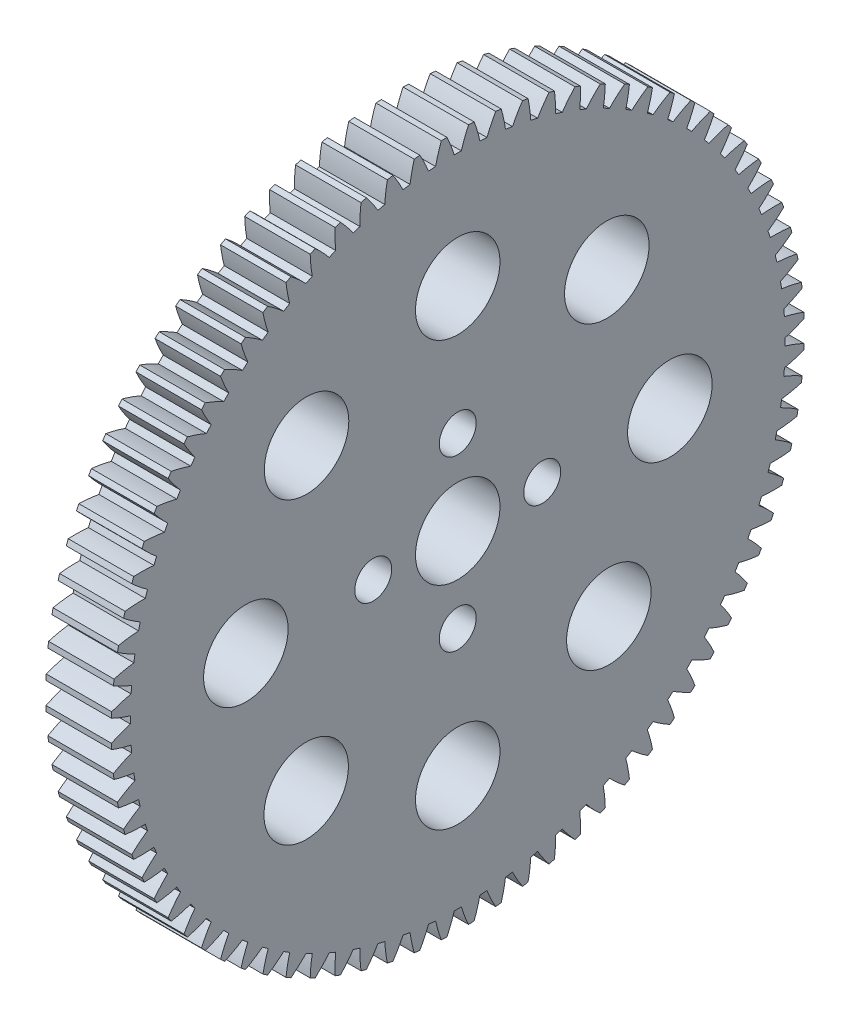
SolidWorks part; units mm, degrees
material "6061 Alloy"
ref_plane "Plane1" through (0, 0, 0) normal (0, 0, 1) x (1, 0, 0)
ref_plane "Plane2" through (0, 0, 0) normal (0, 1, 0) x (1, 0, 0)
ref_plane "Plane3" through (0, 0, 0) normal (1, 0, 0) x (0, 0, -1)
sketch "HoldingSke" plane through (0, 0, 0) normal (0, 1, 0) x (1, 0, 0)
  line L0 (0, 0) -> (0.2171, -1.231)
  line L1 (-15, 0) -> (100, 0) construction
  line L2 (0, 0) -> (-2.1039, 2.3779)
  line L3 (0, 0) -> (-11.863, 4.5341)
  line L4 (0, 0) -> (1.4996, 8.5048)
  line L5 (0, 0) -> (-46.8476, -17.4728)
  line L6 (0, 0) -> (-5.1396, -3.4677)
  line L7 (-2.1039, 2.3779) -> (8.6586, 51.2059)
  line L8 (-76.2, 54.61) -> (-74.8, 54.61)
  line L9 (-71.009, 38.7566) -> (-53.1078, 45.2721)
  line L10 (-76.2, 71.12) -> (104.1128, 71.12)
  line L11 (0, 0) -> (-6.2, 0)
  line L12 (-76.2, 101.6) -> (-76.17, 101.6)
  line L13 (24.9733, 27.94) -> (52.9518, 28.4284)
  line L14 (24.9733, 27.94) -> (24.9743, 27.94)
  line L15 (24.9733, 27.94) -> (100.4006, 29.5858)
  line L16 (-63.627, -0.8) -> (-12.827, -0.8)
  circle A0 centre (0, 0) radius 4
  circle A1 centre (0, 0) radius 30.999
  circle A2 centre (0, 0) radius 37.5
  circle A3 centre (0, 0) radius 4
  dimension "MHD" = 61.998
  dimension "Hub_dia" = 75
  dimension "Bore" = 8
  dimension "MBD" = 8
  dimension "Num_teeth" = 80
  dimension "Pitch_radius" = 180.3128
  dimension "Pitch" = 1.25
  dimension "Width" = 6.2
  dimension "Overall_len" = 50
  dimension "Show_teeth" = 80
  dimension "Thickness" = 6.2
  dimension "OAL" = 50.0001
  dimension "T_dim" = 1.4
  dimension "Ap" = 20
  dimension "H" = 19.05
  dimension "Backlash" = 0.03
  dimension "Addendum_fac" = 1
  dimension "Dedendum_fac" = 1.25
  dimension "Clearance_fac" = 0.25
  dimension "Dedendum_add" = 0.001
  dimension "Module" = 0.8
sketch "BasProSke" plane through (0, 0, 0) normal (0, 1, 0) x (1, 0, 0)
  line L0 (-10, 0) -> (60, 0) construction
  line L1 (0, 0) -> (0, 32.8)
  line L2 (0, 0) -> (6.2, 0)
  line L3 (6.2, 0) -> (6.2, 32.8)
  line L4 (6.2, 32.8) -> (0, 32.8)
  dimension "Diameter" = 65.6
  dimension "Thickness" = 6.2
revolve "Base-Revolve" add sketch "BasProSke" angle 360 about L0
sketch "TooCutSke" plane through (0, 0, 0) normal (1, 0, 0) x (0, 0, -1)
  line L1 (0, 0) -> (0, 107) construction
  line L2 (0, 0) -> (-0.6808, 31.9928) construction
  line L3 (0, 0) -> (-2.5122, 63.9403) construction
  line L4 (-0.6808, 31.9928) -> (-1.2561, 31.9702) construction
  arc A0 (0.3357, 30.9972) -> (-0.3357, 30.9972) centre (0, 0) ccw
  arc A1 (1.0352, 32.8091) -> (-1.0352, 32.8091) centre (0, 0) ccw
  circle A2 centre (0, 0) radius 32 construction
  circle A3 centre (0, 0) radius 30.0702 construction
  arc A4 (-0.3357, 30.9972) -> (-1.0352, 32.8091) centre (-12.5921, 27.3066) ccw
  arc A5 (1.0352, 32.8091) -> (0.3357, 30.9972) centre (12.5921, 27.3066) ccw
  dimension "Root_dia" = 61.998
  dimension "Overcut_dia" = 65.6508
  dimension "Pitch_dia" = 64
  dimension "Base_dia" = 60.1403
  dimension "Flank_rad" = 12.8
  dimension "Half_ang" = 2.25
  dimension "Half_CT" = 0.5758
extrude "ToothCut" cut sketch "TooCutSke" along normal through all
fillet "Breaks" [suppressed] radius 0.016
fillet "RootFillets" [suppressed] radius 0.201
pattern_circular "TeethCuts" count 80 every 4.5 about axis through (-10, 0, 0) along (1, 0, 0) of "ToothCut", "RootFillets", "Breaks"
sketch "HubNeaOneSke" plane through (0, 0, 0) normal (-1, 0, 0) x (0, 0, 1)
  circle A0 centre (0, 0) radius 30.999
  dimension "Diameter" = 61.998
extrude "HubNearOne" [suppressed] add sketch "HubNeaOneSke" along normal blind 43.8001
sketch "HubNeaBotSke" plane through (0, 0, 0) normal (-1, 0, 0) x (0, 0, 1)
  circle A0 centre (0, 0) radius 30.999
  dimension "Diameter" = 61.998
extrude "HubNearBoth" [suppressed] add sketch "HubNeaBotSke" along normal blind 21.9
ref_plane "FarPln" through (6.2, 0, 0) normal (1, 0, 0) x (0, 0, -1)
sketch "HubFarSke" plane through (6.2, 0, 0) normal (1, 0, 0) x (0, 0, -1)
  circle A0 centre (0, 0) radius 30.999
  dimension "Diameter" = 61.998
extrude "HubFar" [suppressed] add sketch "HubFarSke" along normal blind 21.9
sketch "BorSke" plane through (0, 0, 0) normal (1, 0, 0) x (0, 0, -1)
  circle A0 centre (0, 0) radius 4
  dimension "Diameter" = 8
extrude "Bore" cut sketch "BorSke" along normal mid plane 100.0001
sketch "KeySke" plane through (0, 0, 0) normal (1, 0, 0) x (0, 0, -1)
  line L0 (-1.5, 0) -> (-1.5, 5.4)
  line L1 (-1.5, 5.4) -> (1.5, 5.4)
  line L2 (1.5, 5.4) -> (1.5, 0)
  line L3 (0, 0) -> (0, 34) construction
  line L4 (-1.5, 0) -> (1.5, 0)
  dimension "Offset" = 5.4
  dimension "Width" = 3
extrude "Keyway" [suppressed] cut sketch "KeySke" along normal mid plane 100.0001
pattern_circular "Keyway2" [suppressed] count 2 every 90 about axis through (-10, 0, 0) along (1, 0, 0)
sketch "Sketch1" plane through (6.2, 0, 0) normal (1, 0, 0) x (0, 0, -1)
  line L0 (0, 0) -> (28.2252, 28.7327) construction
  line L1 (0, 0) -> (-25.3201, -24.9439) construction
  line L2 (0, 0) -> (24.7366, -24.4515) construction
  line L3 (0, 0) -> (-25.836, 25.5556) construction
  circle A0 centre (0, 20.084) radius 4
  circle A1 centre (0, -20.0633) radius 4
  circle A2 centre (20.084, 0) radius 4
  circle A3 centre (-20.0633, 0) radius 4
  circle A4 centre (14.1126, 14.3663) radius 4
  circle A5 centre (14.3069, -14.142) radius 4
  circle A6 centre (-14.3483, -14.1351) radius 4
  circle A7 centre (-14.315, 14.1597) radius 4
  circle A8 centre (0, 8) radius 1.75
  circle A9 centre (0, -8) radius 1.75
  circle A10 centre (8, 0) radius 1.75
  circle A11 centre (-8, 0) radius 1.75
  dimension "D1" = 8
  dimension "D2" = 8
  dimension "D3" = 8
  dimension "D4" = 8
  dimension "D5" = 8
  dimension "D6" = 8
  dimension "D7" = 8
  dimension "D8" = 8
  dimension "D17" = 3.5
  dimension "D18" = 3.5
  dimension "D19" = 3.5
  dimension "D20" = 3.5
  dimension "D9" = 12.7
  dimension "D10" = 12.7
  dimension "D11" = 12.7
  dimension "D12" = 12.7
  dimension "D13" = 12.7
  dimension "D14" = 12.7
  dimension "D15" = 12.7
  dimension "D16" = 12.7
  dimension "D21" = 8
  dimension "D22" = 8
  dimension "D23" = 8
  dimension "D24" = 8
extrude "Cut-Extrude1" cut sketch "Sketch1" against normal through all
equation "' \"Module@HoldingSke\" = 6.35"
equation "' \"Num_teeth@HoldingSke\" = 12"
equation "' \"Ap@HoldingSke\" =  20"
equation "' \"Width@HoldingSke\" = 0.5 * 25.4"
equation "' \"Hub_dia@HoldingSke\"= 1 * 25.4"
equation "' \"Overall_len@HoldingSke\" = 1.0 * 25.4"
equation "' \"Bore@HoldingSke\" = 0.75 * 25.4"
equation "' \"T_dim@HoldingSke\" = 0.1 * 25.4"
equation "' \"Width@KeySke\" = 0.25 * 25.4"
equation "' \"Show_teeth@HoldingSke\" = 13"
equation "' \"Backlash@HoldingSke\" = 0.009 * 25.4"
equation "' \"Addendum_fac@HoldingSke\" = 1.0"
equation "' \"Dedendum_fac@HoldingSke\" = 1.25"
equation "' \"Dedendum_add@HoldingSke\" = 0.00005 * 25.4"
equation "' \"Clearance_fac@HoldingSke\" = 0.25"
equation "\"Pitch@HoldingSke\" = 1 / \"Module@HoldingSke\""
equation "\"Overcut_dia@TooCutSke\" = (\"Num_teeth@HoldingSke\" + 2 * \"Addendum_fac@HoldingSke\") / \"Pitch@HoldingSke\" + 0.002 * 25.4"
equation "\"Pitch_dia@TooCutSke\" = \"Num_teeth@HoldingSke\" / \"Pitch@HoldingSke\""
equation "\"Base_dia@TooCutSke\" = \"Num_teeth@HoldingSke\" / \"Pitch@HoldingSke\" * cos((\"Ap@HoldingSke\"  * 3.14159265 / 180))"
equation "\"Root_dia@TooCutSke\" = (\"Num_teeth@HoldingSke\" + 2) / \"Pitch@HoldingSke\" - 2 * (\"Addendum_fac@HoldingSke\" + \"Dedendum_fac@HoldingSke\") / \"Pitch@HoldingSke\" - \"Dedendum_add@HoldingSke\" * 2"
equation "\"Half_ang@TooCutSke\" = 180 / \"Num_teeth@HoldingSke\""
equation "\"Half_CT@TooCutSke\" = \"Num_teeth@HoldingSke\" / \"Pitch@HoldingSke\" * sin((3.14159265 / 2 / \"Num_teeth@HoldingSke\")) / 2 - 7 * \"Backlash@HoldingSke\" / 4"
equation "\"Flank_rad@TooCutSke\" = \"Num_teeth@HoldingSke\" / \"Pitch@HoldingSke\" / 5"
equation "\"Radius@RootFillets\" = \"Clearance_fac@HoldingSke\" / \"Pitch@HoldingSke\" + \"Dedendum_add@HoldingSke\""
equation "\"Break_rad@Breaks\" = 0.02 / \"Pitch@HoldingSke\""
equation "\"Thickness@HoldingSke\" = \"Width@HoldingSke\""
equation "\"OAL@HoldingSke\" = \"Thickness@HoldingSke\""
equation "\"MHD@HoldingSke\" = (\"Num_teeth@HoldingSke\" + 2) / \"Pitch@HoldingSke\" - 2 * (\"Addendum_fac@HoldingSke\" + \"Dedendum_fac@HoldingSke\")  / \"Pitch@HoldingSke\" - \"Dedendum_add@HoldingSke\" * 2"
equation "\"MBD@HoldingSke\" = (\"Num_teeth@HoldingSke\" + 2) / \"Pitch@HoldingSke\" - 2 * (\"Addendum_fac@HoldingSke\" + \"Dedendum_fac@HoldingSke\")  / \"Pitch@HoldingSke\" - \"Dedendum_add@HoldingSke\" * 2 - 0.002 * 25.4"
equation "\"MHD@HoldingSke\" = ((sgn( \"MHD@HoldingSke\" - \"Hub_dia@HoldingSke\" )-1)*( \"MHD@HoldingSke\" - \"Hub_dia@HoldingSke\" ))/-2+ \"Hub_dia@HoldingSke\""
equation "\"MBD@HoldingSke\" = ((sgn( \"MBD@HoldingSke\" - \"Bore@HoldingSke\" )-1)*( \"MBD@HoldingSke\" - \"Bore@HoldingSke\" ))/-2+ \"Bore@HoldingSke\""
equation "\"OAL@HoldingSke\" = ((sgn( \"OAL@HoldingSke\" - \"Overall_len@HoldingSke\" )+1)*( \"OAL@HoldingSke\" - \"Overall_len@HoldingSke\" ))/2 + \"Overall_len@HoldingSke\" + 0.000002 * 25.4"
equation "\"Num_teeth@TeethCuts\" = int( \"Show_teeth@HoldingSke\" ) + 1"
equation "\"Num_teeth@TeethCuts\" = ((sgn( \"Num_teeth@TeethCuts\" - \"Num_teeth@HoldingSke\" )-1)*( \"Num_teeth@TeethCuts\" - \"Num_teeth@HoldingSke\" ))/-2+ \"Num_teeth@HoldingSke\""
equation "\"Num_teeth@TeethCuts\" = ((sgn( \"Num_teeth@TeethCuts\" - 2.0)+1)*( \"Num_teeth@TeethCuts\" - 2.0))/2 +2.0"
equation "\"Angle@TeethCuts\" = 360.0 / \"Num_teeth@HoldingSke\""
equation "\"Diameter@BasProSke\" = (\"Num_teeth@HoldingSke\" + 2 * \"Addendum_fac@HoldingSke\") / \"Pitch@HoldingSke\""
equation "\"Thickness@BasProSke\"  = \"Thickness@HoldingSke\""
equation "' \"Fillet_rad@BasProSke\" =  \"Thickness@HoldingSke\" * 0.05"
equation "\"MHD@HoldingSke\" = ((sgn( \"MHD@HoldingSke\" - \"Root_dia@TooCutSke\" )-1)*( \"MHD@HoldingSke\" - \"Root_dia@TooCutSke\" ))/-2+ \"Root_dia@TooCutSke\""
equation "\"Diameter@HubNeaOneSke\" = \"MHD@HoldingSke\""
equation "\"Length@HubNearOne\" = \"OAL@HoldingSke\" - \"Thickness@BasProSke\""
equation "\"Diameter@HubNeaBotSke\" = \"MHD@HoldingSke\""
equation "\"Length@HubNearBoth\" = ( \"OAL@HoldingSke\" - \"Thickness@BasProSke\" ) / 2.0"
equation "\"Thickness@FarPln\" = \"Thickness@BasProSke\""
equation "\"Diameter@HubFarSke\" = \"MHD@HoldingSke\""
equation "\"Length@HubFar\" = ( \"OAL@HoldingSke\" - \"Thickness@BasProSke\" ) / 2.0"
equation "\"Diameter@BorSke\" = \"MBD@HoldingSke\""
equation "\"D1@Bore\" = \"OAL@HoldingSke\" * 2.0"
equation "\"D1@Keyway\" = \"OAL@HoldingSke\" * 2.0"
equation "\"Offset@KeySke\" = \"T_dim@HoldingSke\" + \"MBD@HoldingSke\" / 2.0"
